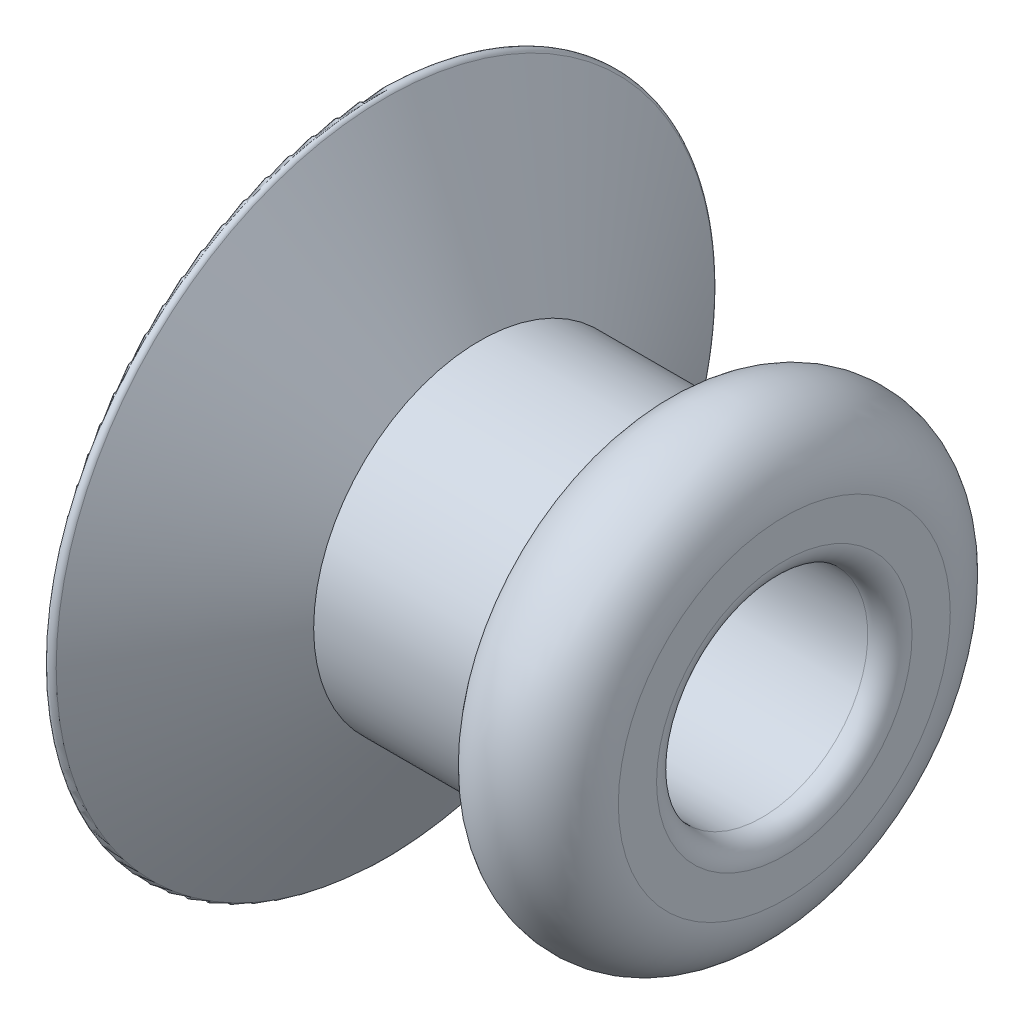
SolidWorks part; units mm, degrees
material "Сталь 10кп ГОСТ 1050-88"
ref_plane "Спереди" through (0, 0, 0) normal (0, 0, 1) x (1, 0, 0)
ref_plane "Сверху" through (0, 0, 0) normal (0, 1, 0) x (1, 0, 0)
ref_plane "Справа" through (0, 0, 0) normal (1, 0, 0) x (0, 0, -1)
sketch "Эскиз2" plane through (0, 0, 0) normal (0, 0, 1) x (1, 0, 0)
  line L0 (0, 0) -> (6, 0) construction
  line L1 (0.599, -2.099) -> (0, -2.099) construction
  line L2 (3.4981, -0.9545) -> (0.2, -0.9545)
  line L3 (0, -0.9545) -> (0, 0) construction
  line L4 (0, -1.1545) -> (0, -2.95)
  line L5 (0.6535, -1.55) -> (1.3891, -1.55) construction
  line L6 (0.0933, -2.975) -> (0.9449, -1.5)
  line L7 (0.9449, -1.5) -> (2.5, -1.5)
  line L8 (3.6981, -1.1545) -> (3.6981, -1.5)
  line L9 (3.099, -1.5) -> (3.6981, -1.5) construction
  line L10 (0, -0.9545) -> (0.9449, -1.5) construction
  line L11 (0.0933, 2.975) -> (0.9449, 1.5) construction
  arc A0 (3.4981, -0.9545) -> (3.6981, -1.1545) centre (3.4981, -1.1545) cw
  arc A1 (2.5, -1.5) -> (3.6981, -1.5) centre (3.099, -1.5) ccw
  arc A2 (0, -2.95) -> (0.0933, -2.975) centre (0.05, -2.95) ccw
  arc A3 (0.2, -0.9545) -> (0, -1.1545) centre (0.2, -1.1545) ccw
  dimension "D4" = 0.2
  dimension "D2" = 120
  dimension "D8" = 0.05
  dimension "D3" = 30
  dimension "D5" = 1.9089
  dimension "D6" = 3
  dimension "D7" = 6
  dimension "D9" = 6
  dimension "D10" = 2.5
  dimension "D11" = 3.1
  dimension "D12" = 0.9449
revolve "Повернуть1" add sketch "Эскиз2" angle 360 about L0
